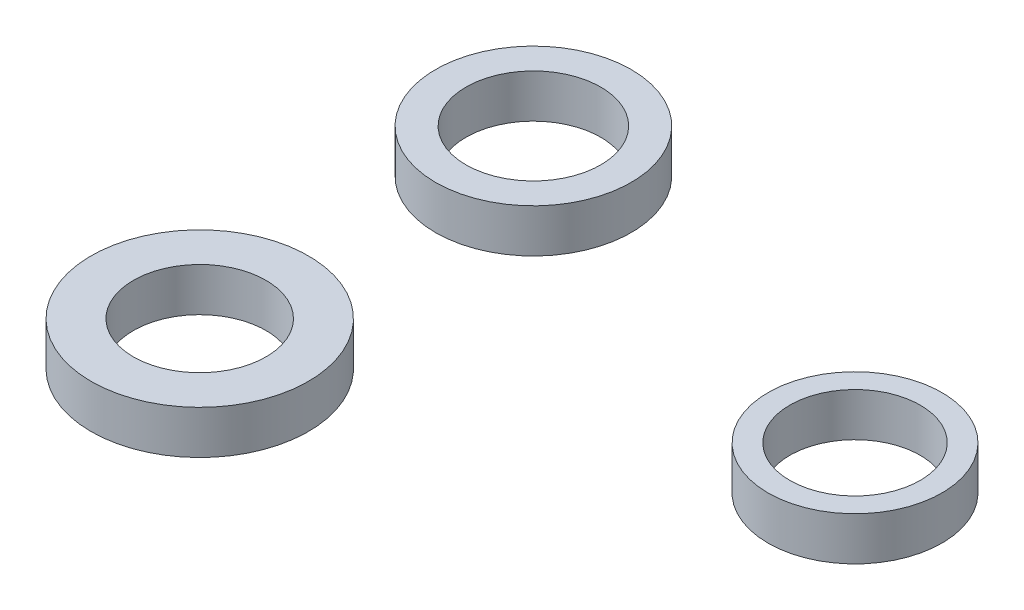
SolidWorks part; units mm, degrees
ref_plane "前视基准面" through (0, 0, 0) normal (0, 0, 1) x (1, 0, 0)
ref_plane "上视基准面" through (0, 0, 0) normal (0, 1, 0) x (1, 0, 0)
ref_plane "右视基准面" through (0, 0, 0) normal (1, 0, 0) x (0, 0, -1)
sketch "草图1" plane through (0, 0, 0) normal (0, 1, 0) x (1, 0, 0)
  circle A0 centre (-33.1031, 2.8407) radius 4
  circle A1 centre (-33.1031, 2.8407) radius 3
  circle A2 centre (-53.1173, 8.0622) radius 3.1
  circle A3 centre (-53.1173, 8.0622) radius 4.5
  circle A4 centre (-53.1173, -7.2832) radius 3.05
  circle A5 centre (-53.1173, -7.2832) radius 5
  dimension "D1" = 8
  dimension "D2" = 6
  dimension "D3" = 6.2
  dimension "D4" = 9
  dimension "D5" = 6.1
  dimension "D6" = 10
extrude "凸台-拉伸1" add sketch "草图1" along normal blind 2
